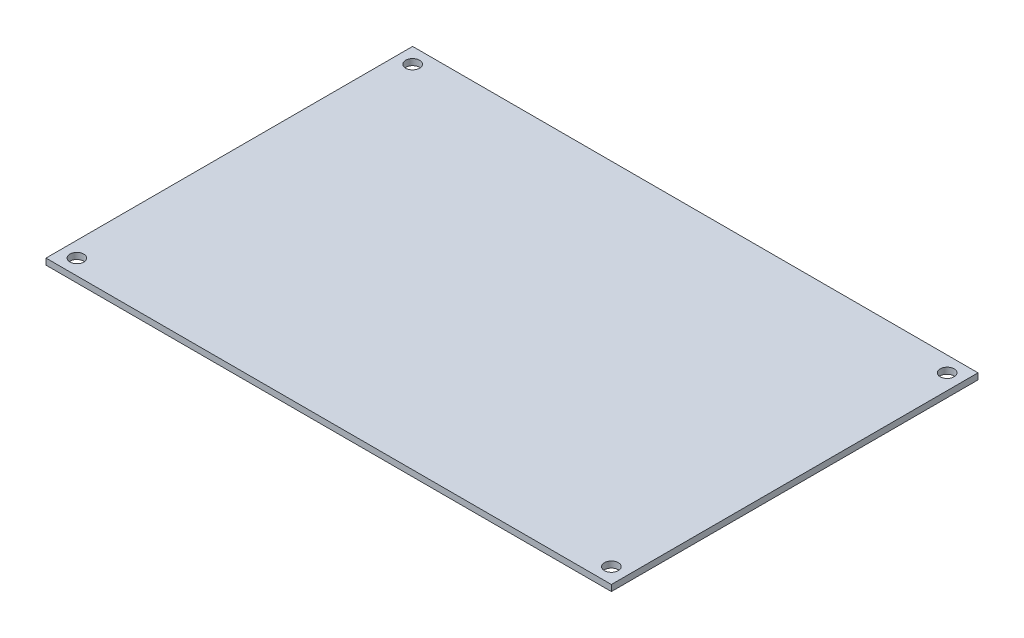
SolidWorks part; units mm, degrees
ref_plane "Front" through (0, 0, 0) normal (0, 0, 1) x (1, 0, 0)
ref_plane "Top" through (0, 0, 0) normal (0, 1, 0) x (1, 0, 0)
ref_plane "Right" through (0, 0, 0) normal (1, 0, 0) x (0, 0, -1)
sketch "Sketch2" plane through (0, 0, 0) normal (0, 1, 0) x (1, 0, 0)
  line L0 (0, 82.799) -> (0, 0) construction
  line L1 (-73.25, 47.5) -> (73.25, 47.5)
  line L2 (-73.25, 47.5) -> (-73.25, -47.5)
  line L3 (-73.25, -47.5) -> (73.25, -47.5)
  line L4 (73.25, 47.5) -> (73.25, -47.5)
  line L5 (0, 0) -> (105.0232, 0) construction
  circle A0 centre (-69.25, 43.5) radius 1.8
  circle A1 centre (69.25, 43.5) radius 1.8
  circle A2 centre (69.25, -43.5) radius 1.8
  circle A3 centre (-69.25, -43.5) radius 1.8
  dimension "D3" = 3.6
  dimension "D1" = 146.5
  dimension "D2" = 95
  dimension "D4" = 4
  dimension "D5" = 4
extrude "Boss-Extrude1" add sketch "Sketch2" against normal blind 1.6
sketch "Sketch4" plane through (0, 0, 0) normal (0, 1, 0) x (1, 0, 0)
  line L0 (0, 86.2063) -> (0, 0) construction
  line L1 (0, 0) -> (74.3902, 0) construction
  circle A0 centre (-69.5, 43.75) radius 1
  circle A1 centre (69.5, 43.75) radius 1
  circle A2 centre (69.5, -43.75) radius 1
  circle A3 centre (-69.5, -43.75) radius 1
  dimension "D3" = 2
  dimension "D1" = 139
  dimension "D2" = 87.5
